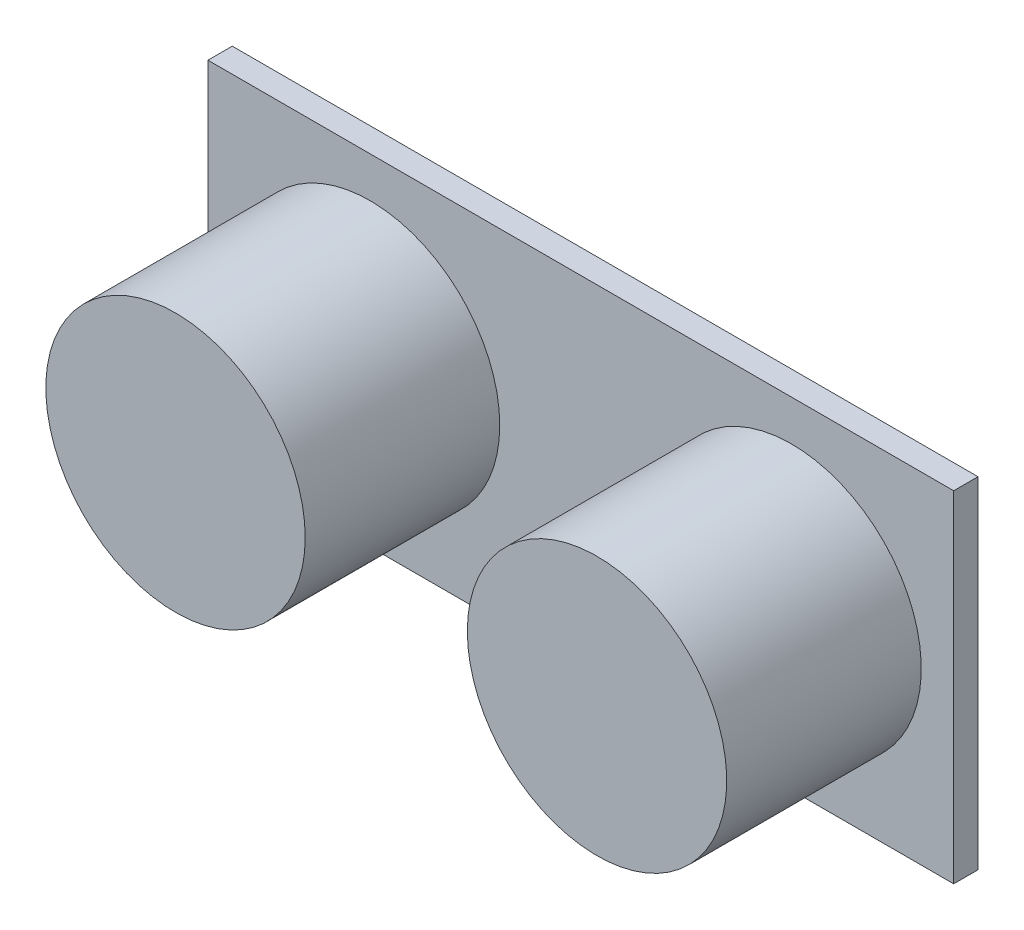
SolidWorks part; units mm, degrees
ref_plane "前视基准面" through (0, 0, 0) normal (0, 0, 1) x (1, 0, 0)
ref_plane "上视基准面" through (0, 0, 0) normal (0, 1, 0) x (1, 0, 0)
ref_plane "右视基准面" through (0, 0, 0) normal (1, 0, 0) x (0, 0, -1)
sketch "草图1" plane through (0, 0, 0) normal (0, 0, 1) x (1, 0, 0)
  line L1 (0, 0) -> (46, 0)
  line L2 (0, 0) -> (0, -21)
  line L3 (0, -21) -> (46, -21)
  line L4 (46, 0) -> (46, -21)
  dimension "D1" = 46
  dimension "D2" = 21
extrude "凸台-拉伸1" add sketch "草图1" along normal blind 1.5
sketch "草图2" plane through (0, 0, 1.5) normal (0, 0, 1) x (1, 0, 0)
  line L0 (0, -10.5) -> (10, -10.5) construction
  line L1 (0, 0) -> (0, -21) construction
  line L2 (10, -10.5) -> (10, -21) construction
  line L3 (0, -21) -> (46, -21) construction
  line L4 (23, -21) -> (23, 0) construction
  line L5 (46, 0) -> (0, 0) construction
  circle A0 centre (10, -10.5) radius 8
  circle A1 centre (36, -10.5) radius 8
  dimension "D2" = 16
  dimension "D1" = 10
extrude "凸台-拉伸2" add sketch "草图2" along normal blind 12
sketch "草图3" plane through (0, 0, 1.5) normal (0, 0, 1) x (1, 0, 0)
  line L0 (0, -21) -> (46, -21) construction
  line L1 (18, -19.4756) -> (28, -19.4756)
  line L2 (18, -19.4756) -> (18, -22.5244)
  line L3 (18, -22.5244) -> (28, -22.5244)
  line L4 (28, -19.4756) -> (28, -22.5244)
  line L5 (18, -19.4756) -> (28, -22.5244) construction
  line L6 (18, -22.5244) -> (28, -19.4756) construction
  point P0 (23, -21)
  dimension "D1" = 10
extrude "凸台-拉伸3" add sketch "草图3" along normal blind 1 and the other way blind 5 separate body
